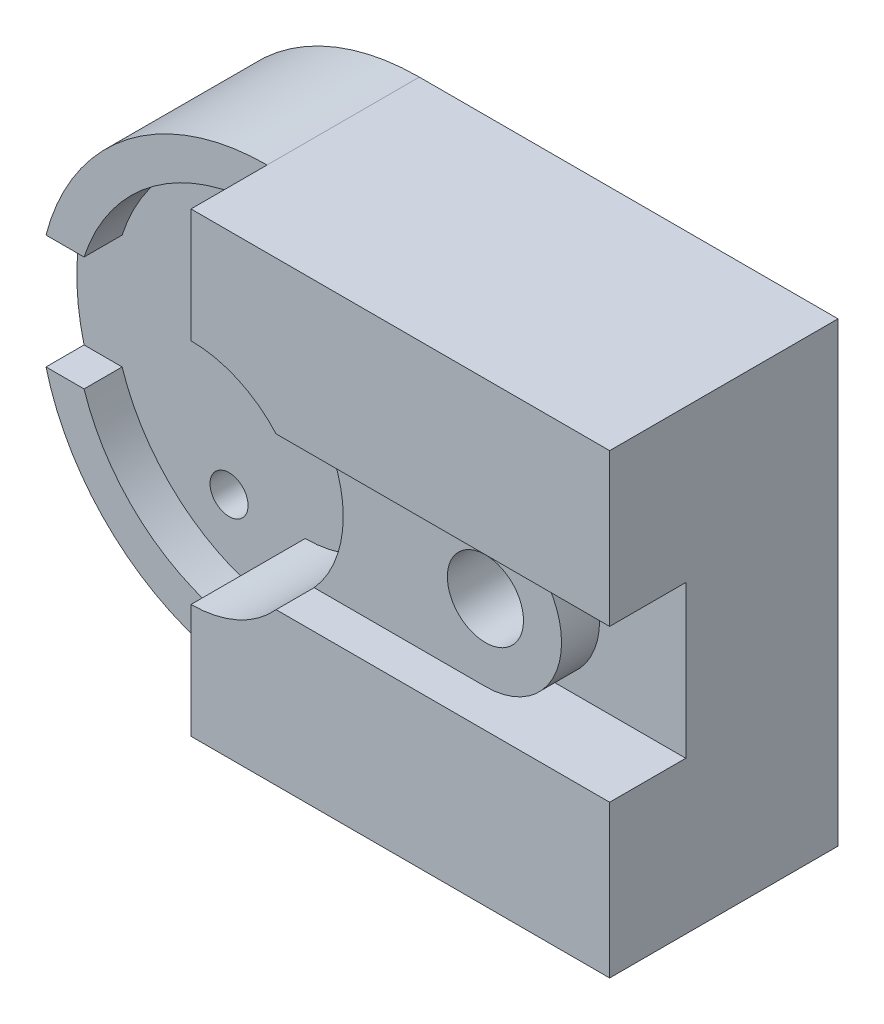
SolidWorks part; units mm, degrees
ref_plane "Front Plane" through (0, 0, 0) normal (0, 0, 1) x (1, 0, 0)
ref_plane "Top Plane" through (0, 0, 0) normal (0, 1, 0) x (1, 0, 0)
ref_plane "Right Plane" through (0, 0, 0) normal (1, 0, 0) x (0, 0, -1)
sketch "Sketch2" plane through (0, 0, 0) normal (0, 0, 1) x (1, 0, 0)
  line L0 (-55, 0) -> (0, 0)
  line L1 (0, 0) -> (0, 60)
  line L2 (0, 60) -> (-55, 60)
  arc A0 (-55, 60) -> (-55, 0) centre (-55, 30) ccw
  dimension "D1" = 30
  dimension "D2" = 55
extrude "Boss-Extrude4" add sketch "Sketch2" along normal blind 15
sketch "Sketch5" plane through (0, 0, 15) normal (0, 0, 1) x (1, 0, 0)
  line L0 (-84.0474, 37.5) -> (-79.0474, 37.5)
  line L1 (-55, 60) -> (-55, 55)
  line L2 (-55, 0) -> (-55, 5)
  line L3 (-84.0474, 22.5) -> (-79.0474, 22.5)
  arc A1 (-55, 60) -> (-55, 0) centre (-55, 30) ccw construction
  arc A2 (-79.0474, 37.5) -> (-55, 55) centre (-55, 29.7278) cw
  arc A3 (-79.0474, 22.5) -> (-55, 5) centre (-55, 30.2722) ccw
  arc A4 (-84.0474, 22.5) -> (-55, 0) centre (-55, 30) ccw
  arc A5 (-84.0474, 37.5) -> (-55, 60) centre (-55, 30) cw
  dimension "D2" = 5
  dimension "D6" = 30
  dimension "D7" = 30
  dimension "D1" = 5
  dimension "D3" = 5
  dimension "D4" = 5
  dimension "D5" = 15
extrude "Boss-Extrude5" add sketch "Sketch5" along normal blind 5
sketch "Sketch6" plane through (0, 0, 15) normal (0, 0, 1) x (1, 0, 0)
  line L0 (-55, 60) -> (-55, 45)
  line L1 (0, 60) -> (-55, 60) construction
  line L2 (-55, 0) -> (-55, 15)
  line L3 (-55, 0) -> (0, 0) construction
  line L4 (-55, 0) -> (0, 0)
  line L5 (0, 60) -> (0, 0)
  line L6 (0, 60) -> (-55, 60)
  line L7 (0, 0) -> (0, 60) construction
  arc A0 (-55, 15) -> (-55, 45) centre (-55, 30) ccw
  dimension "D2" = 15
  dimension "D1" = 55
  dimension "D3" = 15
  dimension "D5" = 15
  dimension "D8" = 55
extrude "Boss-Extrude8" add sketch "Sketch6" along normal blind 15
sketch "Sketch9" plane through (0, 0, 30) normal (0, 0, 1) x (1, 0, 0)
  line L0 (-43.8197, 40) -> (0, 40)
  line L1 (0, 0) -> (0, 60) construction
  line L2 (-43.8197, 20) -> (0, 20)
  line L3 (0, 20) -> (0, 40)
  arc A0 (-43.8197, 40) -> (-43.8197, 20) centre (-55, 30) cw
  arc A1 (-55, 15) -> (-55, 45) centre (-55, 30) ccw construction
  dimension "D2" = 15
  dimension "D1" = 20
extrude "Cut-Extrude2" cut sketch "Sketch9" against normal blind 10
sketch "Sketch10" plane through (0, 0, 20) normal (0, 0, 1) x (1, 0, 0)
  line L1 (-43.8197, 40) -> (-21.3197, 40)
  line L2 (0, 40) -> (-43.8197, 40) construction
  line L3 (-21.3197, 20) -> (-43.8197, 20)
  arc A0 (-43.8197, 20) -> (-43.8197, 40) centre (-55, 30) ccw
  arc A1 (-21.3197, 40) -> (-21.3197, 20) centre (-21.3197, 30) cw
  dimension "D1" = 15
  dimension "D2" = 22.5
extrude "Boss-Extrude9" add sketch "Sketch10" along normal blind 5
sketch "Sketch11" plane through (0, 0, 25) normal (0, 0, 1) x (1, 0, 0)
  circle A0 centre (-21.3197, 30) radius 5
  arc A1 (-21.3197, 20) -> (-21.3197, 40) centre (-21.3197, 30) ccw construction
  point P7 (-11.3197, 30)
  dimension "D2" = 10
  dimension "D1" = 10
extrude "Cut-Extrude3" cut sketch "Sketch11" against normal blind 54
sketch "Sketch12" plane through (0, 0, 15) normal (0, 0, 1) x (1, 0, 0)
  line L0 (0, 60) -> (-55, 60) construction
  circle A0 centre (-55, 30) radius 5
  circle A1 centre (-65, 15) radius 2.5
  circle A2 centre (-65, 45) radius 2.5
  dimension "D1" = 10
  dimension "D4" = 5
  dimension "D7" = 5
  dimension "D8" = 30
  dimension "D2" = 15
  dimension "D3" = 10
  dimension "D5" = 15
  dimension "D6" = 10
extrude "Cut-Extrude4" cut sketch "Sketch12" against normal blind 76
